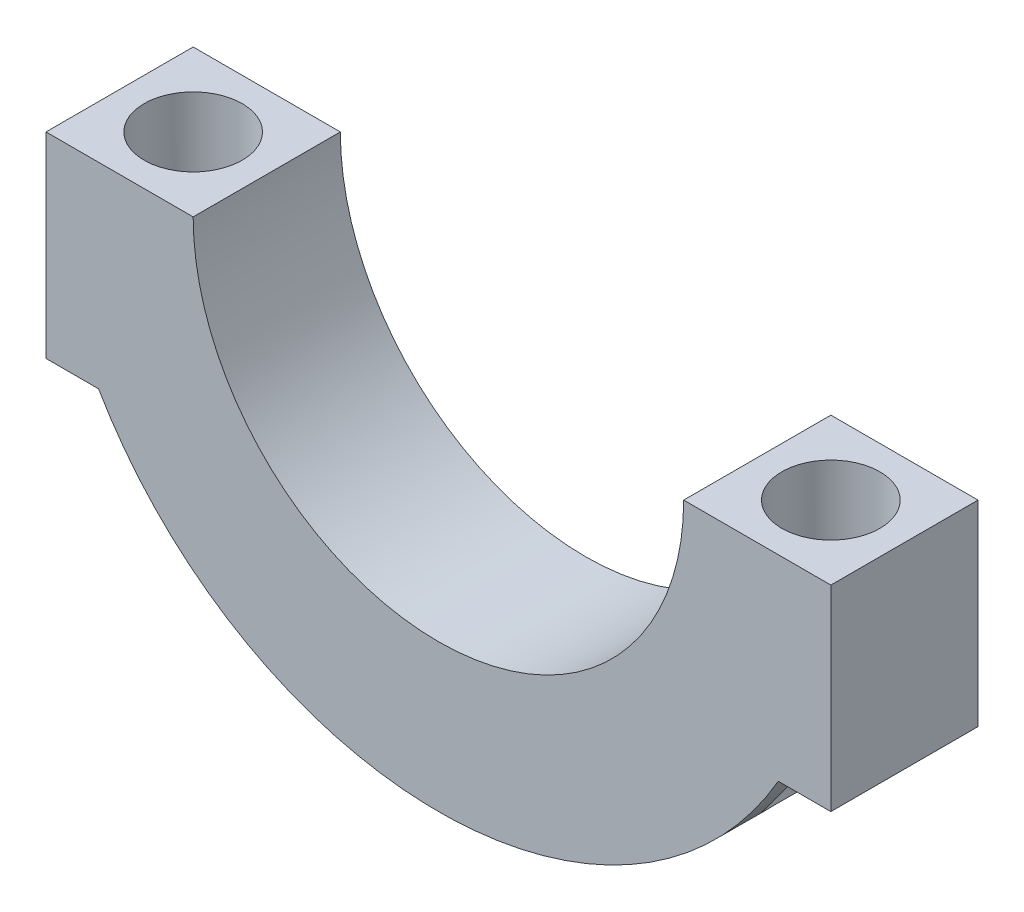
SolidWorks part; units mm, degrees
ref_plane "Front Plane" through (0, 0, 0) normal (0, 0, 1) x (1, 0, 0)
ref_plane "Top Plane" through (0, 0, 0) normal (0, 1, 0) x (1, 0, 0)
ref_plane "Right Plane" through (0, 0, 0) normal (1, 0, 0) x (0, 0, -1)
sketch "Sketch2" plane through (0, 0, 0) normal (0, 0, 1) x (1, 0, 0)
  line L0 (25, 0) -> (-25, 0) construction
  line L1 (0, 0) -> (0, 38.2933) construction
  line L6 (-40, 0) -> (-25, 0)
  line L11 (40, 0) -> (25, 0)
  line L15 (-40, 0) -> (-40, -20)
  line L16 (-40, -20) -> (-34.641, -20)
  line L19 (40, 0) -> (40, -20)
  line L20 (40, -20) -> (34.641, -20)
  arc A2 (25, 0) -> (-25, 0) centre (0, 0) cw
  arc A3 (34.641, -20) -> (-34.641, -20) centre (0, 0) cw
  dimension "D1" = 25
  dimension "D2" = 20
  dimension "D3" = 15
extrude "Boss-Extrude4" add sketch "Sketch2" along normal blind 15
sketch "Sketch5" plane through (0, 0, 0) normal (0, 1, 0) x (1, 0, 0)
  line L0 (0, 0) -> (0, 40.5826) construction
  circle A2 centre (-32.5, -7.5) radius 5
  circle A3 centre (32.5, -7.5) radius 5
  dimension "D1" = 10
extrude "Cut-Extrude1" cut sketch "Sketch5" against normal through all
